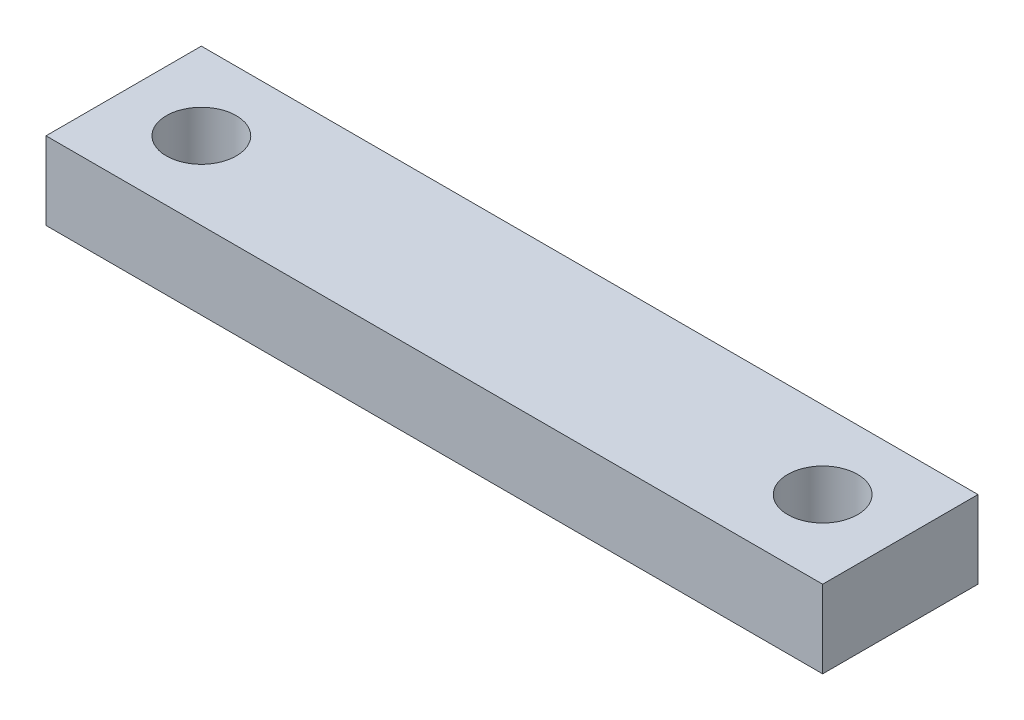
SolidWorks part; units mm, degrees
ref_plane "Front Plane" through (0, 0, 0) normal (0, 0, 1) x (1, 0, 0)
ref_plane "Top Plane" through (0, 0, 0) normal (0, 1, 0) x (1, 0, 0)
ref_plane "Right Plane" through (0, 0, 0) normal (1, 0, 0) x (0, 0, -1)
sketch "Sketch1" plane through (0, 0, 0) normal (0, 1, 0) x (1, 0, 0)
  line L0 (-25, -5) -> (25, -5)
  line L1 (-25, -5) -> (-25, 5)
  line L2 (25, -5) -> (25, 5)
  line L3 (-25, 5) -> (25, 5)
  line L4 (-25, 5) -> (25, -5) construction
  line L5 (25, -5) -> (25.6881, -6.3529) construction
  line L6 (20, 0) -> (0, 0) construction
  line L7 (0, 0) -> (-20, 0) construction
  circle A0 centre (-20, 0) radius 2.25
  circle A1 centre (20, 0) radius 2.25
  dimension "D3" = 4.5
  dimension "D4" = 40
  dimension "D1" = 50
  dimension "D2" = 10
extrude "Boss-Extrude1" add sketch "Sketch1" along normal blind 5
